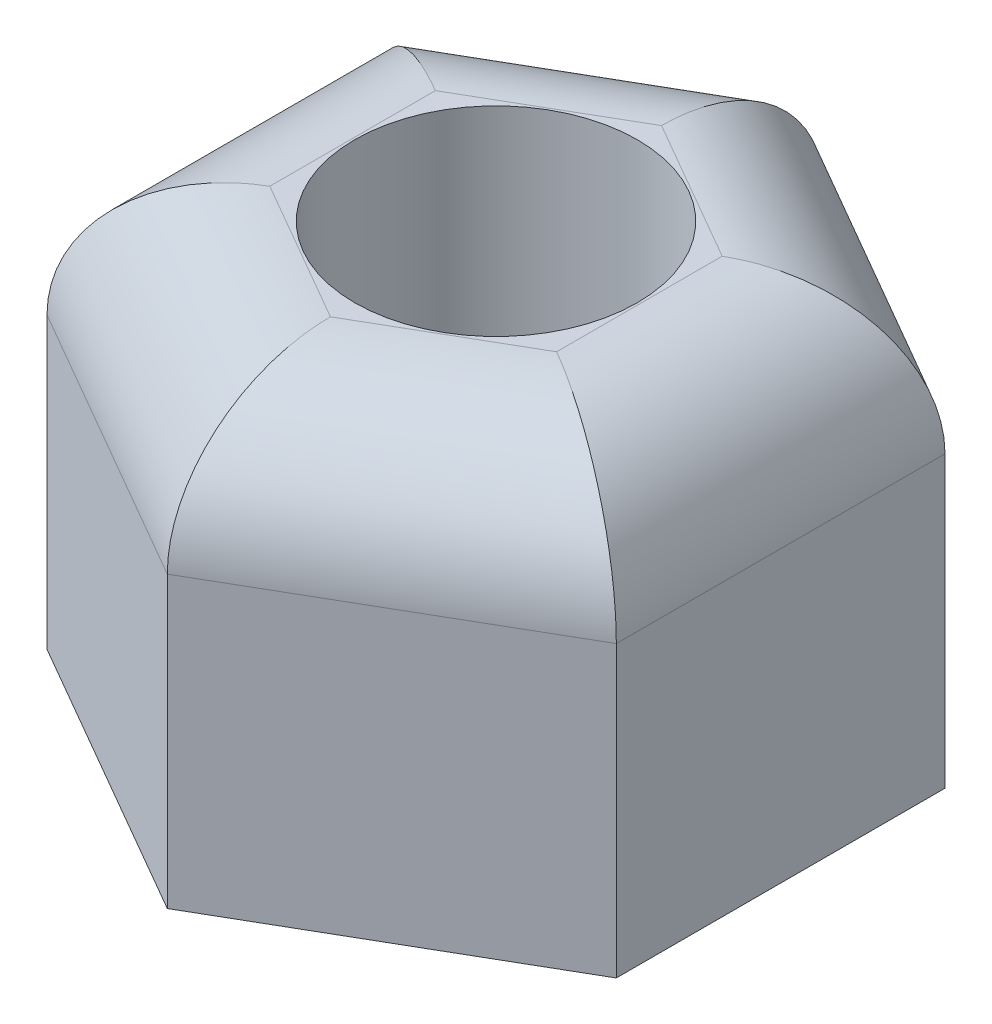
SolidWorks part; units mm, degrees
ref_plane "Front Plane" through (0, 0, 0) normal (0, 0, 1) x (1, 0, 0)
ref_plane "Top Plane" through (0, 0, 0) normal (0, 1, 0) x (1, 0, 0)
ref_plane "Right Plane" through (0, 0, 0) normal (1, 0, 0) x (0, 0, -1)
sketch "Sketch1" plane through (0, 0, 0) normal (0, 1, 0) x (1, 0, 0)
  line L1 (2.015, 1.1634) -> (0, 2.3267)
  line L2 (0, 2.3267) -> (-2.015, 1.1634)
  line L3 (-2.015, 1.1634) -> (-2.015, -1.1634)
  line L4 (-2.015, -1.1634) -> (0, -2.3267)
  line L5 (0, -2.3267) -> (2.015, -1.1634)
  line L6 (2.015, -1.1634) -> (2.015, 1.1634)
  circle A0 centre (0, 0) radius 2.015 construction
  circle A1 centre (0, 0) radius 1
  dimension "D1" = 4.03
  dimension "D2" = 2
extrude "Boss-Extrude1" add sketch "Sketch1" along normal blind 3.05 contours L4 L5 L6 L1 L2 L3
fillet "Fillet1" radius 1 6 edges at (-2.015, 3.05, 0) (-1.0075, 3.05, -1.745) (1.0075, 3.05, -1.745) (2.015, 3.05, 0) (1.0075, 3.05, 1.745) (-1.0075, 3.05, 1.745)
